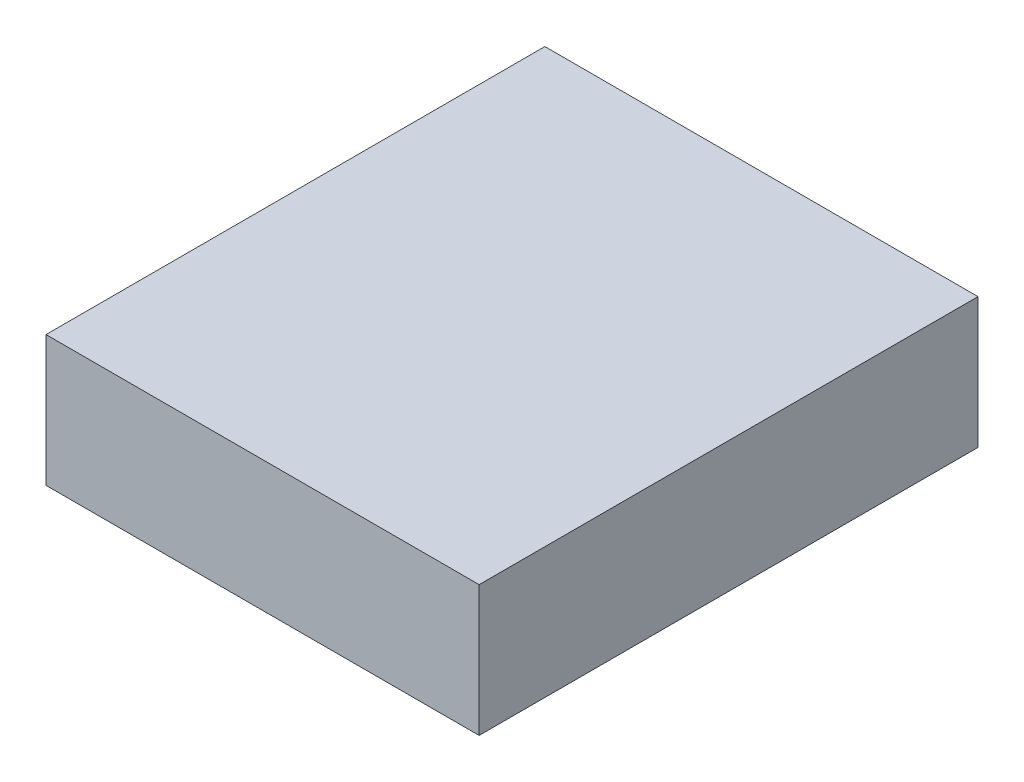
SolidWorks part; units mm, degrees
ref_plane "Front Plane" through (0, 0, 0) normal (0, 0, 1) x (1, 0, 0)
ref_plane "Top Plane" through (0, 0, 0) normal (0, 1, 0) x (1, 0, 0)
ref_plane "Right Plane" through (0, 0, 0) normal (1, 0, 0) x (0, 0, -1)
sketch "Sketch1" plane through (0, 0, 0) normal (0, 1, 0) x (1, 0, 0)
  line L1 (0, 0) -> (65.278, 0)
  line L2 (0, 0) -> (0, 75.184)
  line L3 (0, 75.184) -> (65.278, 75.184)
  line L4 (65.278, 0) -> (65.278, 75.184)
  point P7 (0, 0)
  point P9 (0, 8.3271)
  point P10 (14.7766, 9.5214)
  point P11 (8.8156, 8.7475)
  dimension "D1" = 65.278
  dimension "D2" = 75.184
extrude "Boss-Extrude1" add sketch "Sketch1" along normal blind 19.685
sketch "Sketch3" plane through (0, 0, 0) normal (0, -1, 0) x (1, 0, 0)
  line L0 (0, 0) -> (65.278, 0) construction
  line L1 (0, -75.184) -> (0, 0) construction
  circle A0 centre (16.51, -6.604) radius 2.54
  dimension "D2" = 5.08
  dimension "D1" = 6.604
  dimension "D3" = 16.51
extrude "Boss-Extrude2" add sketch "Sketch3" along normal blind 3.302
